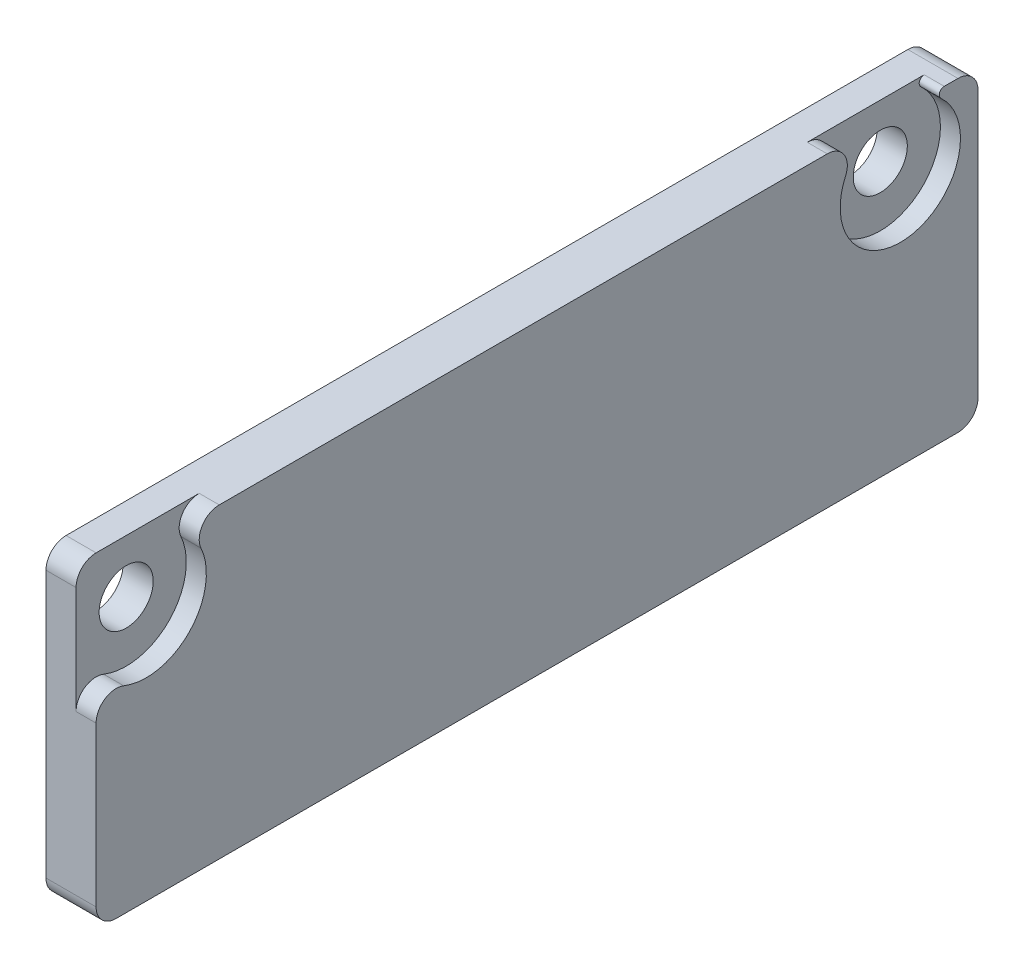
SolidWorks part; units mm, degrees
material "ABS"
ref_plane "Front Plane" through (0, 0, 0) normal (0, 0, 1) x (1, 0, 0)
ref_plane "Top Plane" through (0, 0, 0) normal (0, 1, 0) x (1, 0, 0)
ref_plane "Right Plane" through (0, 0, 0) normal (1, 0, 0) x (0, 0, -1)
sketch "Sketch1" plane through (0, 0, 0) normal (1, 0, 0) x (0, 0, -1)
  line L0 (-19.5, 5) -> (18.125, 5) construction
  line L1 (-22, -7.65) -> (22, -7.65)
  line L2 (-22, -7.65) -> (-22, 7.65)
  line L3 (-22, 7.65) -> (22, 7.65)
  line L4 (22, -7.65) -> (22, 7.65)
  line L5 (-22, -7.65) -> (22, 7.65) construction
  line L6 (-22, 7.65) -> (22, -7.65) construction
  point P0 (0, 0)
  dimension "D1" = 15.3
  dimension "D2" = 44
  dimension "D3" = 2.65
  dimension "D4" = 2.5
  dimension "D5" = 3.875
extrude "Boss-Extrude1" add sketch "Sketch1" along normal blind 2.5
hole_wizard "CBORE for M2.5 Pan Head Machine Screw1" positions "Sketch3" profile "Sketch4" counterbore size "M2.5" standard "ANSI Metric" end condition through all
sketch "Sketch3" plane through (2.5, 0, 0) normal (1, 0, 0) x (0, 0, -1)
  point P0 (-19.5, 5)
  point P3 (18.125, 5)
sketch "Sketch4" plane through (2.5, 5, 19.5) normal (0, 1, 0) x (0, 0, -1)
  line L0 (0, 0) -> (0, 2.5)
  line L1 (0, 2.5) -> (1.35, 2.5)
  line L3 (1.35, 2.5) -> (1.35, 1)
  line L4 (1.35, 1) -> (3, 1)
  line L5 (3, 1) -> (3, 0)
  line L7 (3, 0) -> (0, 0)
  line L11 (0, -6.35) -> (0, 107.95) construction
  dimension "Thru Hole Dia." = 2.7
  dimension "Thru Hole Depth" = 2.5
  dimension "C'Bore Dia." = 6
  dimension "C'Bore Depth" = 1
sketch "Sketch5" plane through (2.5, 0, 0) normal (1, 0, 0) x (0, 0, -1)
  line L2 (-22, 7.65) -> (-22, 6.6583)
  line L3 (-20.9062, 7.65) -> (-22, 7.65)
  line L4 (-22, 7.65) -> (-22, 6.6583)
  line L5 (-20.9062, 7.65) -> (-22, 7.65)
  line L6 (-22, 7.65) -> (-22, 6.6583)
  line L7 (-22, 7.65) -> (-22, 6.6583)
  line L10 (-20.9062, 7.65) -> (-22, 7.65)
  line L11 (-20.9062, 7.65) -> (-22, 7.65)
  arc A1 (-20.9062, 7.65) -> (-22, 6.6583) centre (-19.5, 5) ccw
  arc A2 (-20.9062, 7.65) -> (-22, 6.6583) centre (-19.5, 5) ccw
  arc A3 (-20.9062, 7.65) -> (-22, 6.6583) centre (-19.5, 5) ccw
  arc A5 (-20.9062, 7.65) -> (-22, 6.6583) centre (-19.5, 5) ccw
  dimension "D1" = 0
  dimension "D2" = 0
extrude "Cut-Extrude1" cut sketch "Sketch5" against normal up to surface (1 mm away) contours A2 L5 L4 up to face at (1.5, 5, 18.15)
fillet "Fillet1" radius 1 7 edges at (2, 7.65, -16.7188) (2, 3.3417, 22) (2, 7.65, 18.0938) (0.75, 7.65, 22) (1.25, 7.65, -22) (1.25, -7.65, -22) (1.25, -7.65, 22)
fillet "Fillet2" radius 0.25 1 edges at (2, 7.65, -19.5312)
